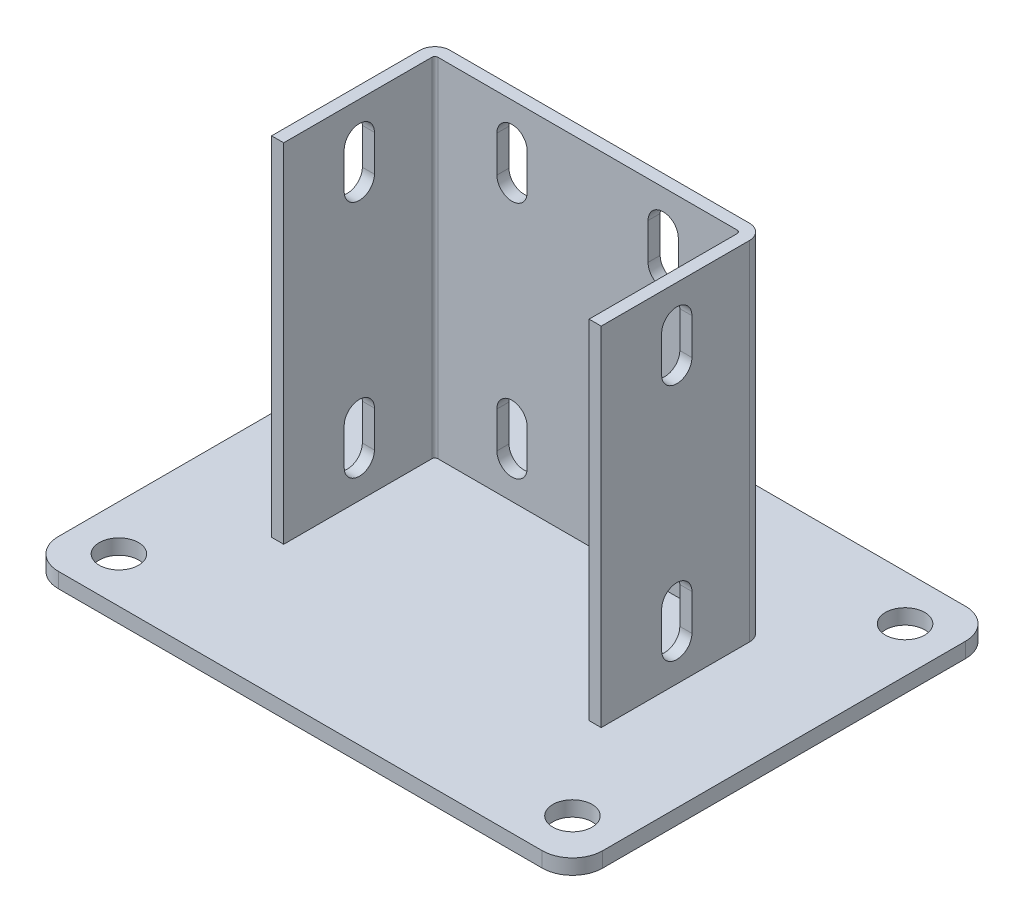
SolidWorks part; units mm, degrees
material "Ст3пс ГОСТ 380-2005"
ref_plane "Спереди" through (0, 0, 0) normal (0, 0, 1) x (1, 0, 0)
ref_plane "Сверху" through (0, 0, 0) normal (0, 1, 0) x (1, 0, 0)
ref_plane "Справа" through (0, 0, 0) normal (1, 0, 0) x (0, 0, -1)
sketch "Эскиз2" plane through (0, 0, 0) normal (0, 1, 0) x (1, 0, 0)
  line L1 (-90, -70) -> (90, -70)
  line L2 (-90, -70) -> (-90, 70)
  line L3 (-90, 70) -> (90, 70)
  line L4 (90, -70) -> (90, 70)
  line L5 (-90, -70) -> (90, 70) construction
  line L6 (-90, 70) -> (90, -70) construction
  point P0 (0, 0)
  dimension "D1" = 140
  dimension "D2" = 180
extrude "Бобышка-Вытянуть1" add sketch "Эскиз2" along normal blind 5
sketch "Эскиз3" plane through (0, 5, 0) normal (0, 1, 0) x (1, 0, 0)
  line L0 (-50.5, -25) -> (-50.5, 25)
  line L1 (-50.5, 25) -> (50.5, 25)
  line L2 (50.5, 25) -> (50.5, -25)
  point P2 (0, 25)
  point P5 (-50.5, 0)
  dimension "D2" = 101
  dimension "D3" = 50
extrude "Вытянуть-Тонкостенный1" add sketch "Эскиз3" along normal offset from surface (115 mm away) 120 thin up to face at (0, 0, 0) thin type one direction reverse wall 4
sketch "Эскиз4" plane through (0, 0, 0) normal (1, 0, 0) x (0, 0, -1)
  line L0 (29, 67.3538) -> (65, 5)
  line L1 (29, 120) -> (29, 5) construction
  line L2 (-70, 5) -> (70, 5) construction
  line L3 (65, 5) -> (29, 5)
  line L4 (29, 5) -> (29, 67.3538)
  line L5 (70, 5) -> (70, 0) construction
  dimension "D1" = 30
  dimension "D2" = 5
extrude "Бобышка-Вытянуть2" add sketch "Эскиз4" along normal mid plane 4
sketch "Эскиз5" plane through (54.5, 0, 0) normal (1, 0, 0) x (0, 0, -1)
  line L0 (0, 108) -> (0, 96) construction
  line L1 (5, 108) -> (5, 96)
  line L2 (-5, 108) -> (-5, 96)
  line L3 (0, 29) -> (0, 17) construction
  line L4 (5, 29) -> (5, 17)
  line L5 (-5, 29) -> (-5, 17)
  line L6 (-25, 120) -> (24, 120) construction
  line L7 (-70, 5) -> (70, 5) construction
  arc A0 (5, 108) -> (-5, 108) centre (0, 108) ccw
  arc A1 (-5, 96) -> (5, 96) centre (0, 96) ccw
  arc A2 (5, 29) -> (-5, 29) centre (0, 29) ccw
  arc A3 (-5, 17) -> (5, 17) centre (0, 17) ccw
  point P3 (0, 102)
  point P8 (0, 23)
  dimension "D2" = 12
  dimension "D4" = 12
  dimension "D1" = 10
  dimension "D3" = 12
extrude "Вырез-Вытянуть1" cut sketch "Эскиз5" against normal through all
sketch "Эскиз6" plane through (0, 5, 0) normal (0, 1, 0) x (1, 0, 0)
  line L0 (-90, 70) -> (-90, -70) construction
  line L1 (75, -55) -> (-75, -55) construction
  line L2 (75, -55) -> (75, 55) construction
  line L3 (75, 55) -> (-75, 55) construction
  line L4 (-75, -55) -> (-75, 55) construction
  line L5 (75, -55) -> (-75, 55) construction
  line L6 (75, 55) -> (-75, -55) construction
  line L7 (90, 70) -> (-90, 70) construction
  circle A0 centre (-75, 55) radius 6.5
  circle A1 centre (-75, -55) radius 6.5
  circle A2 centre (75, 55) radius 6.5
  circle A3 centre (75, -55) radius 6.5
  point P0 (0, 0)
  dimension "D1" = 13
  dimension "D2" = 15
  dimension "D3" = 15
extrude "Вырез-Вытянуть2" cut sketch "Эскиз6" against normal through all
fillet "Скругление1" radius 10 4 edges at (90, 2.5, 70) (-90, 2.5, 70) (-90, 2.5, -70) (90, 2.5, -70)
sketch "Эскиз8" plane through (0, 0, -29) normal (0, 0, -1) x (-1, 0, 0)
  line L0 (-25, 108) -> (-25, 96) construction
  line L1 (-20, 108) -> (-20, 96)
  line L2 (-30, 108) -> (-30, 96)
  line L3 (-25, 29) -> (-25, 17) construction
  line L4 (-20, 29) -> (-20, 17)
  line L5 (-30, 29) -> (-30, 17)
  line L6 (-49.5, 120) -> (49.5, 120) construction
  line L7 (-80, 5) -> (80, 5) construction
  line L8 (0, 0) -> (0, 120) construction
  line L9 (-80, 0) -> (80, 0) construction
  line L10 (25, 108) -> (25, 96) construction
  line L11 (20, 108) -> (20, 96)
  line L12 (30, 108) -> (30, 96)
  line L13 (25, 29) -> (25, 17) construction
  line L14 (20, 29) -> (20, 17)
  line L15 (30, 29) -> (30, 17)
  arc A0 (-20, 108) -> (-30, 108) centre (-25, 108) ccw
  arc A1 (-30, 96) -> (-20, 96) centre (-25, 96) ccw
  arc A2 (-20, 29) -> (-30, 29) centre (-25, 29) ccw
  arc A3 (-30, 17) -> (-20, 17) centre (-25, 17) ccw
  arc A4 (20, 108) -> (30, 108) centre (25, 108) cw
  arc A5 (30, 96) -> (20, 96) centre (25, 96) cw
  arc A6 (20, 29) -> (30, 29) centre (25, 29) cw
  arc A7 (30, 17) -> (20, 17) centre (25, 17) cw
  point P2 (-25, 102)
  point P7 (-25, 23)
  point P24 (25, 102)
  point P31 (25, 23)
  dimension "D3" = 12
  dimension "D4" = 12
  dimension "D1" = 10
  dimension "D2" = 12
  dimension "D5" = 40
extrude "Вырез-Вытянуть3" cut sketch "Эскиз8" against normal up to next
